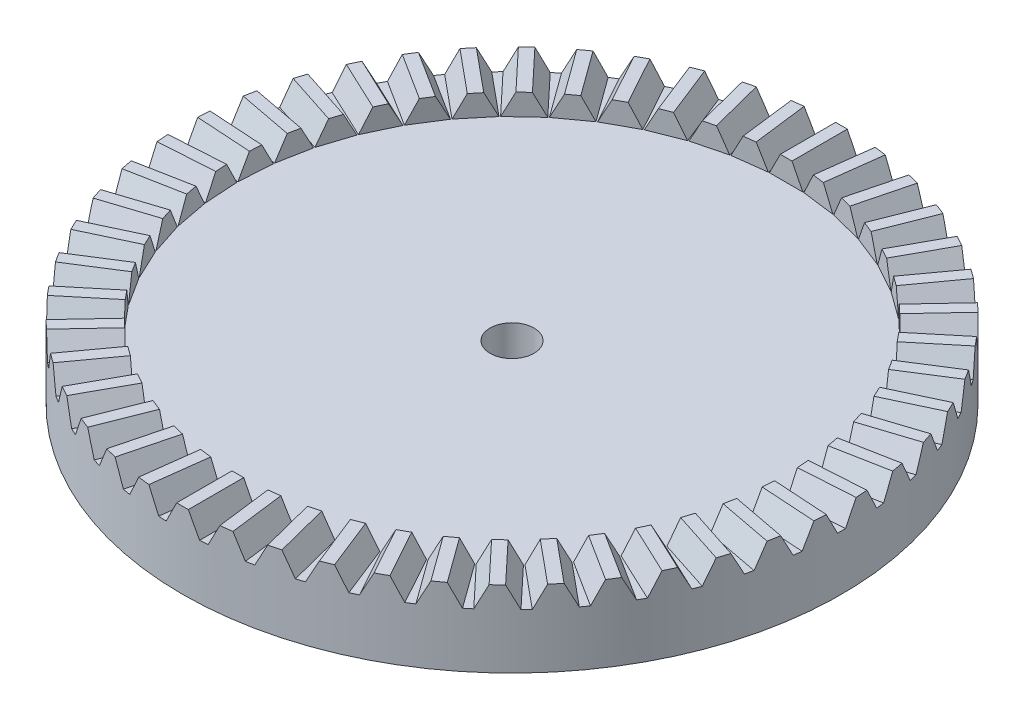
SolidWorks part; units mm, degrees
ref_plane "Front Plane" through (0, 0, 0) normal (0, 0, 1) x (1, 0, 0)
ref_plane "Top Plane" through (0, 0, 0) normal (0, 1, 0) x (1, 0, 0)
ref_plane "Right Plane" through (0, 0, 0) normal (1, 0, 0) x (0, 0, -1)
sketch "Foot Measurements" [suppressed] plane through (0, 0, 0) normal (0, 1, 0) x (1, 0, 0)
  line L0 (0, 0) -> (0, 73) construction
  line L1 (0, 0) -> (0, 147) construction
  line L2 (0, 0) -> (33, 0) construction
  line L3 (0, 0) -> (75, 0) construction
  line L4 (0, 73) -> (33, 73) construction
  line L5 (33, 73) -> (33, 0) construction
  line L6 (0, 147) -> (75, 147) construction
  line L7 (75, 147) -> (75, 0) construction
  line L8 (0, -100) -> (250, -100) construction
  line L9 (0, -100) -> (173, -100) construction
  dimension "D1" = 33
  dimension "D2" = 75
  dimension "D3" = 73
  dimension "D4" = 147
sketch "Sketch3" plane through (0, 0, 0) normal (0, 1, 0) x (1, 0, 0)
  circle A0 centre (0, 0) radius 30
extrude "Boss-Extrude3" add sketch "Sketch3" along normal blind 5
sketch "Sketch6" plane through (0, 5, 0) normal (0, 1, 0) x (1, 0, 0)
  circle A1 centre (0, 0) radius 2
  dimension "D1" = 4
extrude "Cut-Extrude1" cut sketch "Sketch6" against normal up to next
sketch "Sketch5" plane through (0, 5, 0) normal (0, 1, 0) x (1, 0, 0)
  line L3 (-1.5701, 29.9589) -> (-1.5701, 24.9589)
  line L4 (0, 0) -> (-1.5701, 29.9589) construction
  line L5 (0, 0) -> (1.5701, 29.9589) construction
  line L6 (-1.5701, 24.9589) -> (1.5701, 24.9589)
  line L7 (1.5701, 24.9589) -> (1.5701, 29.9589)
  arc A0 (1.5701, 29.9589) -> (-1.5701, 29.9589) centre (0, 0) ccw
  dimension "D2" = 5
  dimension "D1" = 6
  dimension "D3" = 3.1402
extrude "Boss-Extrude5" add sketch "Sketch5" along normal blind 3
sketch "Sketch14" plane through (0, 0, -24.9589) normal (0, 0, 1) x (1, 0, 0)
  line L1 (-1.5701, 5) -> (-1.5701, 8)
  line L2 (-1.5701, 8) -> (1.5701, 8)
  line L3 (1.5701, 5) -> (1.5201, 5)
  line L4 (1.5701, 8) -> (1.5701, 5)
  line L5 (1.5201, 5) -> (0.532, 6.95)
  line L6 (-1.5701, 5) -> (-1.5201, 5)
  line L7 (-1.5201, 5) -> (-0.532, 6.95)
  line L10 (0.532, 6.95) -> (-0.532, 6.95)
  dimension "D1" = 1.05
  dimension "D2" = 0.05
  dimension "D3" = 53.742
  dimension "D4" = 1.0381
extrude "Cut-Extrude4" cut sketch "Sketch14" against normal up to next (5.0411 mm away) contours L10 L5 L3 L4 L2 L1 L6 L7
pattern_circular "CirPattern2" count 50 over 360 about axis through (0, 0, 0) along (0, 1, 0) of "Cut-Extrude4", "Boss-Extrude5"
